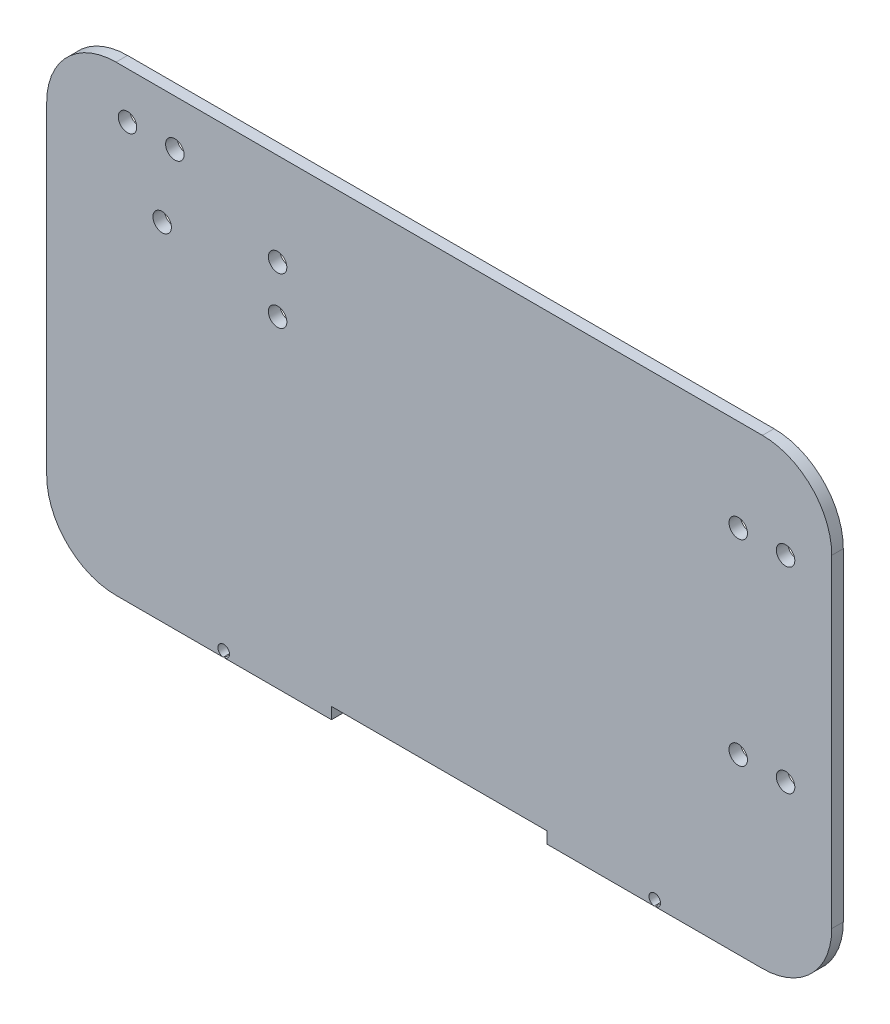
SolidWorks part; units mm, degrees
ref_plane "Alzado" through (0, 0, 0) normal (0, 0, 1) x (1, 0, 0)
ref_plane "Planta" through (0, 0, 0) normal (0, 1, 0) x (1, 0, 0)
ref_plane "Vista lateral" through (0, 0, 0) normal (1, 0, 0) x (0, 0, -1)
sketch "Croquis1" plane through (0, 0, 0) normal (0, 0, 1) x (1, 0, 0)
  line L0 (-125.4724, -88.3321) -> (154.5276, -88.3321)
  line L1 (184.5276, -58.3321) -> (184.5276, 81.6679)
  line L2 (154.5276, 111.6679) -> (-125.4724, 111.6679)
  line L3 (-155.4724, 81.6679) -> (-155.4724, -58.3321)
  arc A0 (-155.4724, -58.3321) -> (-125.4724, -88.3321) centre (-125.4724, -58.3321) ccw
  arc A1 (154.5276, -88.3321) -> (184.5276, -58.3321) centre (154.5276, -58.3321) ccw
  arc A2 (184.5276, 81.6679) -> (154.5276, 111.6679) centre (154.5276, 81.6679) ccw
  arc A3 (-125.4724, 111.6679) -> (-155.4724, 81.6679) centre (-125.4724, 81.6679) ccw
  circle A4 centre (-105.4724, 61.6679) radius 4
  circle A5 centre (-55.4724, 71.6679) radius 4
  circle A6 centre (-55.4724, 51.1679) radius 4
  circle A7 centre (144.0276, -13.3321) radius 4
  circle A8 centre (164.5276, -13.3321) radius 4
  circle A9 centre (144.0276, 71.6679) radius 4
  circle A10 centre (164.5276, 71.6679) radius 4
  circle A11 centre (-99.9724, 91.6679) radius 4
  circle A12 centre (-120.4724, 91.6679) radius 4
  dimension "D1" = 8
  dimension "D2" = 30
  dimension "D3" = 144.0276
  dimension "D4" = 164.5276
  dimension "D5" = 184.5276
  dimension "D6" = 55.4724
  dimension "D7" = 99.9724
  dimension "D8" = 105.4724
  dimension "D9" = 120.4724
  dimension "D10" = 155.4724
  dimension "D11" = 51.1679
  dimension "D12" = 61.6679
  dimension "D13" = 71.6679
  dimension "D14" = 91.6679
  dimension "D15" = 111.6679
  dimension "D16" = 13.3321
  dimension "D17" = 88.3321
extrude "Saliente-Extruir1" add sketch "Croquis1" along normal blind 5
sketch "Croquis3" plane through (0, 0, 5) normal (0, 0, 1) x (1, 0, 0)
  line L0 (-32.1391, -83.3321) -> (-32.1391, -88.3321)
  line L1 (-125.4724, -88.3321) -> (154.5276, -88.3321)
  line L2 (-125.4724, -88.3321) -> (-125.4724, -83.3321)
  line L3 (-125.4724, -83.3321) -> (154.5276, -83.3321)
  line L4 (154.5276, -88.3321) -> (154.5276, -83.3321)
  line L5 (61.1942, -83.3321) -> (61.1942, -88.3321)
  line M10 (-125.4724, -88.3321) -> (154.5276, -88.3321)
  dimension "D1" = 5
  dimension "D2" = 93.3333
  dimension "D3" = 93.3333
extrude "Cortar-Extruir1" cut sketch "Croquis3" against normal blind 10 contours L5 L3 L0 M10
sketch "Croquis6" plane through (0, 0, 5) normal (0, 0, 1) x (1, 0, 0)
  line L0 (-78.8058, -88.3321) -> (-78.8058, -85.8421) construction
  line L1 (-125.4724, -88.3321) -> (-32.1391, -88.3321) construction
  line L2 (14.5276, -83.3321) -> (14.5276, -88.3321) construction
  line L3 (-32.1391, -83.3321) -> (61.1942, -83.3321) construction
  circle A0 centre (-78.8058, -85.8421) radius 2.5
  circle A1 centre (107.8609, -85.8421) radius 2.5
  dimension "D2" = 5
  dimension "D1" = 2.49
extrude "Cortar-Extruir2" cut sketch "Croquis6" against normal blind 10
